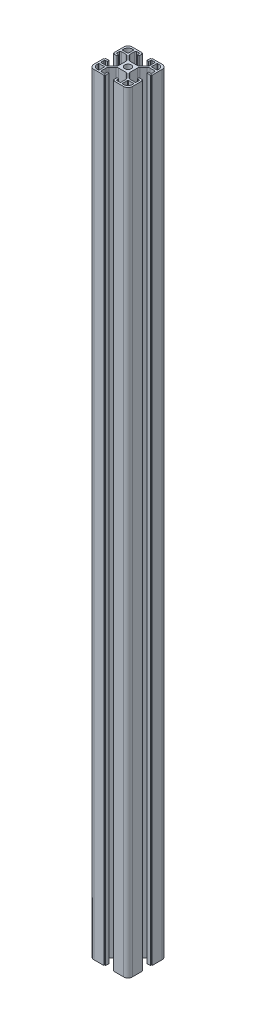
SolidWorks part; units mm, degrees
ref_plane "Front Plane" through (0, 0, 0) normal (0, 0, 1) x (1, 0, 0)
ref_plane "Top Plane" through (0, 0, 0) normal (0, 1, 0) x (1, 0, 0)
ref_plane "Right Plane" through (0, 0, 0) normal (1, 0, 0) x (0, 0, -1)
sketch "Sketch1" plane through (0, 0, 0) normal (0, 1, 0) x (1, 0, 0)
  line L0 (84.1702, 31.7204) -> (84.1702, 42.1204)
  line L1 (44.1702, 62.7204) -> (44.1702, 52.3204)
  line L2 (48.6702, 27.2204) -> (59.0702, 27.2204)
  line L3 (79.6702, 67.2204) -> (69.2702, 67.2204)
  line L4 (84.1702, 52.3204) -> (84.1702, 62.7204)
  line L6 (44.1702, 42.1204) -> (44.1702, 31.7204)
  line L7 (69.2702, 27.2204) -> (79.6702, 27.2204)
  line L10 (44.1702, 42.1204) -> (44.7702, 42.1204)
  line L11 (44.9702, 42.3204) -> (44.9702, 42.9204)
  line L12 (48.6702, 43.1204) -> (45.1702, 43.1204)
  line L13 (48.6702, 41.3204) -> (48.6702, 43.1204)
  line L14 (46.9702, 41.3204) -> (48.6702, 41.3204)
  line L15 (45.9702, 37.9704) -> (45.9702, 40.3204)
  line L16 (51.6169, 36.9704) -> (46.9702, 36.9704)
  line L17 (57.2915, 41.4024) -> (53.7382, 37.8491)
  line L18 (58.1702, 50.9171) -> (58.1702, 43.5237)
  line L19 (53.7382, 56.5917) -> (57.2915, 53.0384)
  line L20 (46.9702, 57.4704) -> (51.6169, 57.4704)
  line L21 (45.9702, 54.1204) -> (45.9702, 56.4704)
  line L22 (48.6702, 53.1204) -> (46.9702, 53.1204)
  line L23 (48.6702, 51.3204) -> (48.6702, 53.1204)
  line L24 (45.1702, 51.3204) -> (48.6702, 51.3204)
  line L25 (44.9702, 51.5204) -> (44.9702, 52.1204)
  line L26 (44.7702, 52.3204) -> (44.1702, 52.3204)
  line L28 (59.0702, 67.2204) -> (48.6702, 67.2204)
  line L29 (59.0702, 67.2204) -> (59.0702, 66.6204)
  line L30 (59.2702, 66.4204) -> (60.0702, 66.4204)
  line L31 (60.0702, 62.7204) -> (60.0702, 66.4204)
  line L32 (58.2702, 62.7204) -> (60.0702, 62.7204)
  line L33 (58.2702, 64.4204) -> (58.2702, 62.7204)
  line L34 (54.9202, 65.4204) -> (57.2702, 65.4204)
  line L35 (53.9202, 59.7737) -> (53.9202, 64.4204)
  line L36 (58.3522, 54.0991) -> (54.7989, 57.6524)
  line L37 (67.8669, 53.2204) -> (60.4735, 53.2204)
  line L38 (73.5415, 57.6524) -> (69.9882, 54.0991)
  line L39 (74.4202, 64.4204) -> (74.4202, 59.7737)
  line L40 (71.0702, 65.4204) -> (73.4202, 65.4204)
  line L41 (70.0702, 62.7204) -> (70.0702, 64.4204)
  line L42 (68.2702, 62.7204) -> (70.0702, 62.7204)
  line L43 (68.2702, 66.2204) -> (68.2702, 62.7204)
  line L44 (68.4702, 66.4204) -> (69.2702, 66.4204)
  line L45 (69.2702, 66.4204) -> (69.2702, 67.2204)
  line L48 (84.1702, 52.3204) -> (83.5702, 52.3204)
  line L49 (83.3702, 52.1204) -> (83.3702, 51.5204)
  line L50 (79.6702, 51.3204) -> (83.1702, 51.3204)
  line L51 (79.6702, 53.1204) -> (79.6702, 51.3204)
  line L52 (81.3702, 53.1204) -> (79.6702, 53.1204)
  line L53 (82.3702, 56.4704) -> (82.3702, 54.1204)
  line L54 (76.7235, 57.4704) -> (81.3702, 57.4704)
  line L55 (71.0489, 53.0384) -> (74.6022, 56.5917)
  line L56 (70.1702, 43.5237) -> (70.1702, 50.9171)
  line L57 (74.6022, 37.8491) -> (71.0489, 41.4024)
  line L58 (81.3702, 36.9704) -> (76.7235, 36.9704)
  line L59 (82.3702, 40.3204) -> (82.3702, 37.9704)
  line L60 (79.6702, 41.3204) -> (81.3702, 41.3204)
  line L61 (79.6702, 43.1204) -> (79.6702, 41.3204)
  line L62 (83.1702, 43.1204) -> (79.6702, 43.1204)
  line L63 (83.3702, 42.9204) -> (83.3702, 42.3204)
  line L64 (83.5702, 42.1204) -> (84.1702, 42.1204)
  line L67 (69.2702, 27.2204) -> (69.2702, 27.8204)
  line L68 (69.0702, 28.0204) -> (68.4702, 28.0204)
  line L69 (68.2702, 31.7204) -> (68.2702, 28.2204)
  line L70 (70.0702, 31.7204) -> (68.2702, 31.7204)
  line L71 (70.0702, 30.0204) -> (70.0702, 31.7204)
  line L72 (73.4202, 29.0204) -> (71.0702, 29.0204)
  line L73 (74.4202, 34.6671) -> (74.4202, 30.0204)
  line L74 (69.9882, 40.3417) -> (73.5415, 36.7884)
  line L75 (60.4735, 41.2204) -> (67.8669, 41.2204)
  line L76 (54.7989, 36.7884) -> (58.3522, 40.3417)
  line L77 (53.9202, 30.0204) -> (53.9202, 34.6671)
  line L78 (57.2702, 29.0204) -> (54.9202, 29.0204)
  line L79 (58.2702, 31.7204) -> (58.2702, 30.0204)
  line L80 (60.0702, 31.7204) -> (58.2702, 31.7204)
  line L81 (60.0702, 28.2204) -> (60.0702, 31.7204)
  line L82 (59.8702, 28.0204) -> (59.2702, 28.0204)
  line L83 (59.0702, 27.8204) -> (59.0702, 27.2204)
  line L84 (82.3702, 34.6704) -> (82.3702, 33.5204)
  line L85 (76.7202, 35.1704) -> (81.8702, 35.1704)
  line L86 (76.2202, 29.5204) -> (76.2202, 34.6704)
  line L87 (77.8702, 29.0204) -> (76.7202, 29.0204)
  line L88 (51.6202, 29.0204) -> (50.4702, 29.0204)
  line L89 (52.1202, 34.6704) -> (52.1202, 29.5204)
  line L90 (46.4702, 35.1704) -> (51.6202, 35.1704)
  line L91 (45.9702, 33.5204) -> (45.9702, 34.6704)
  line L92 (45.9702, 59.7704) -> (45.9702, 60.9204)
  line L93 (51.6202, 59.2704) -> (46.4702, 59.2704)
  line L94 (52.1202, 64.9204) -> (52.1202, 59.7704)
  line L95 (50.4702, 65.4204) -> (51.6202, 65.4204)
  line L96 (76.7202, 65.4204) -> (77.8702, 65.4204)
  line L97 (76.2202, 59.7704) -> (76.2202, 64.9204)
  line L98 (81.8702, 59.2704) -> (76.7202, 59.2704)
  line L99 (82.3702, 60.9204) -> (82.3702, 59.7704)
  arc A0 (60.7702, 47.2204) -> (67.5702, 47.2204) centre (64.1702, 47.2204) ccw
  arc A1 (44.1702, 31.7204) -> (48.6702, 27.2204) centre (48.6702, 31.7204) ccw
  arc A2 (44.7702, 42.1204) -> (44.9702, 42.3204) centre (44.7702, 42.3204) ccw
  arc A3 (45.1702, 43.1204) -> (44.9702, 42.9204) centre (45.1702, 42.9204) ccw
  arc A4 (46.9702, 41.3204) -> (45.9702, 40.3204) centre (46.9702, 40.3204) ccw
  arc A5 (45.9702, 37.9704) -> (46.9702, 36.9704) centre (46.9702, 37.9704) ccw
  arc A6 (51.6169, 36.9704) -> (53.7382, 37.8491) centre (51.6169, 39.9704) ccw
  arc A7 (57.2915, 41.4024) -> (58.1702, 43.5237) centre (55.1702, 43.5237) ccw
  arc A8 (58.1702, 50.9171) -> (57.2915, 53.0384) centre (55.1702, 50.9171) ccw
  arc A9 (53.7382, 56.5917) -> (51.6169, 57.4704) centre (51.6169, 54.4704) ccw
  arc A10 (46.9702, 57.4704) -> (45.9702, 56.4704) centre (46.9702, 56.4704) ccw
  arc A11 (45.9702, 54.1204) -> (46.9702, 53.1204) centre (46.9702, 54.1204) ccw
  arc A12 (44.9702, 51.5204) -> (45.1702, 51.3204) centre (45.1702, 51.5204) ccw
  arc A13 (44.9702, 52.1204) -> (44.7702, 52.3204) centre (44.7702, 52.1204) ccw
  arc A14 (48.6702, 67.2204) -> (44.1702, 62.7204) centre (48.6702, 62.7204) ccw
  arc A15 (59.0702, 66.6204) -> (59.2702, 66.4204) centre (59.2702, 66.6204) ccw
  arc A16 (58.2702, 64.4204) -> (57.2702, 65.4204) centre (57.2702, 64.4204) ccw
  arc A17 (54.9202, 65.4204) -> (53.9202, 64.4204) centre (54.9202, 64.4204) ccw
  arc A18 (53.9202, 59.7737) -> (54.7989, 57.6524) centre (56.9202, 59.7737) ccw
  arc A19 (58.3522, 54.0991) -> (60.4735, 53.2204) centre (60.4735, 56.2204) ccw
  arc A20 (67.8669, 53.2204) -> (69.9882, 54.0991) centre (67.8669, 56.2204) ccw
  arc A21 (73.5415, 57.6524) -> (74.4202, 59.7737) centre (71.4202, 59.7737) ccw
  arc A22 (74.4202, 64.4204) -> (73.4202, 65.4204) centre (73.4202, 64.4204) ccw
  arc A23 (71.0702, 65.4204) -> (70.0702, 64.4204) centre (71.0702, 64.4204) ccw
  arc A24 (68.4702, 66.4204) -> (68.2702, 66.2204) centre (68.4702, 66.2204) ccw
  arc A25 (84.1702, 62.7204) -> (79.6702, 67.2204) centre (79.6702, 62.7204) ccw
  arc A26 (83.5702, 52.3204) -> (83.3702, 52.1204) centre (83.5702, 52.1204) ccw
  arc A27 (83.1702, 51.3204) -> (83.3702, 51.5204) centre (83.1702, 51.5204) ccw
  arc A28 (81.3702, 53.1204) -> (82.3702, 54.1204) centre (81.3702, 54.1204) ccw
  arc A29 (82.3702, 56.4704) -> (81.3702, 57.4704) centre (81.3702, 56.4704) ccw
  arc A30 (76.7235, 57.4704) -> (74.6022, 56.5917) centre (76.7235, 54.4704) ccw
  arc A31 (71.0489, 53.0384) -> (70.1702, 50.9171) centre (73.1702, 50.9171) ccw
  arc A32 (70.1702, 43.5237) -> (71.0489, 41.4024) centre (73.1702, 43.5237) ccw
  arc A33 (74.6022, 37.8491) -> (76.7235, 36.9704) centre (76.7235, 39.9704) ccw
  arc A34 (81.3702, 36.9704) -> (82.3702, 37.9704) centre (81.3702, 37.9704) ccw
  arc A35 (82.3702, 40.3204) -> (81.3702, 41.3204) centre (81.3702, 40.3204) ccw
  arc A36 (83.3702, 42.9204) -> (83.1702, 43.1204) centre (83.1702, 42.9204) ccw
  arc A37 (83.3702, 42.3204) -> (83.5702, 42.1204) centre (83.5702, 42.3204) ccw
  arc A38 (79.6702, 27.2204) -> (84.1702, 31.7204) centre (79.6702, 31.7204) ccw
  arc A39 (69.2702, 27.8204) -> (69.0702, 28.0204) centre (69.0702, 27.8204) ccw
  arc A40 (68.2702, 28.2204) -> (68.4702, 28.0204) centre (68.4702, 28.2204) ccw
  arc A41 (70.0702, 30.0204) -> (71.0702, 29.0204) centre (71.0702, 30.0204) ccw
  arc A42 (73.4202, 29.0204) -> (74.4202, 30.0204) centre (73.4202, 30.0204) ccw
  arc A43 (74.4202, 34.6671) -> (73.5415, 36.7884) centre (71.4202, 34.6671) ccw
  arc A44 (69.9882, 40.3417) -> (67.8669, 41.2204) centre (67.8669, 38.2204) ccw
  arc A45 (60.4735, 41.2204) -> (58.3522, 40.3417) centre (60.4735, 38.2204) ccw
  arc A46 (54.7989, 36.7884) -> (53.9202, 34.6671) centre (56.9202, 34.6671) ccw
  arc A47 (53.9202, 30.0204) -> (54.9202, 29.0204) centre (54.9202, 30.0204) ccw
  arc A48 (57.2702, 29.0204) -> (58.2702, 30.0204) centre (57.2702, 30.0204) ccw
  arc A49 (59.8702, 28.0204) -> (60.0702, 28.2204) centre (59.8702, 28.2204) ccw
  arc A50 (59.2702, 28.0204) -> (59.0702, 27.8204) centre (59.2702, 27.8204) ccw
  arc A51 (82.3702, 34.6704) -> (81.8702, 35.1704) centre (81.8702, 34.6704) ccw
  arc A52 (76.7202, 35.1704) -> (76.2202, 34.6704) centre (76.7202, 34.6704) ccw
  arc A53 (76.2202, 29.5204) -> (76.7202, 29.0204) centre (76.7202, 29.5204) ccw
  arc A54 (77.8702, 29.0204) -> (82.3702, 33.5204) centre (77.8702, 33.5204) ccw
  arc A55 (51.6202, 29.0204) -> (52.1202, 29.5204) centre (51.6202, 29.5204) ccw
  arc A56 (52.1202, 34.6704) -> (51.6202, 35.1704) centre (51.6202, 34.6704) ccw
  arc A57 (46.4702, 35.1704) -> (45.9702, 34.6704) centre (46.4702, 34.6704) ccw
  arc A58 (45.9702, 33.5204) -> (50.4702, 29.0204) centre (50.4702, 33.5204) ccw
  arc A59 (45.9702, 59.7704) -> (46.4702, 59.2704) centre (46.4702, 59.7704) ccw
  arc A60 (51.6202, 59.2704) -> (52.1202, 59.7704) centre (51.6202, 59.7704) ccw
  arc A61 (52.1202, 64.9204) -> (51.6202, 65.4204) centre (51.6202, 64.9204) ccw
  arc A62 (50.4702, 65.4204) -> (45.9702, 60.9204) centre (50.4702, 60.9204) ccw
  arc A63 (76.7202, 65.4204) -> (76.2202, 64.9204) centre (76.7202, 64.9204) ccw
  arc A64 (76.2202, 59.7704) -> (76.7202, 59.2704) centre (76.7202, 59.7704) ccw
  arc A65 (81.8702, 59.2704) -> (82.3702, 59.7704) centre (81.8702, 59.7704) ccw
  arc A66 (82.3702, 60.9204) -> (77.8702, 65.4204) centre (77.8702, 60.9204) ccw
  arc A67 (67.5702, 47.2204) -> (60.7702, 47.2204) centre (64.1702, 47.2204) ccw
extrude "Boss-Extrude2" add sketch "Sketch1" along normal blind 800
ref_plane "Plane2" through (71.0489, 0, -53.0384) normal (0.7071, 0, -0.7071) x (-0.7071, 0, -0.7071)
